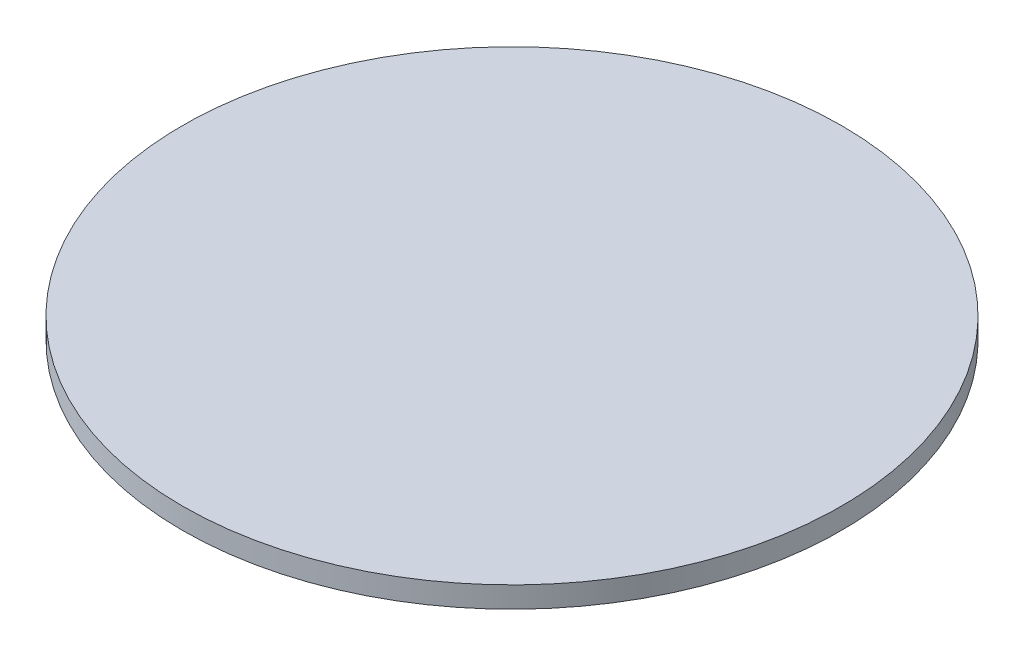
SolidWorks part; units mm, degrees
ref_plane "Front Plane" through (0, 0, 0) normal (0, 0, 1) x (1, 0, 0)
ref_plane "Top Plane" through (0, 0, 0) normal (0, 1, 0) x (1, 0, 0)
ref_plane "Right Plane" through (0, 0, 0) normal (1, 0, 0) x (0, 0, -1)
sketch "Sketch1" plane through (0, 0, 0) normal (0, 1, 0) x (1, 0, 0)
  circle A0 centre (0, 0) radius 62.5
  dimension "D1" = 125
extrude "Boss-Extrude1" add sketch "Sketch1" along normal blind 4
